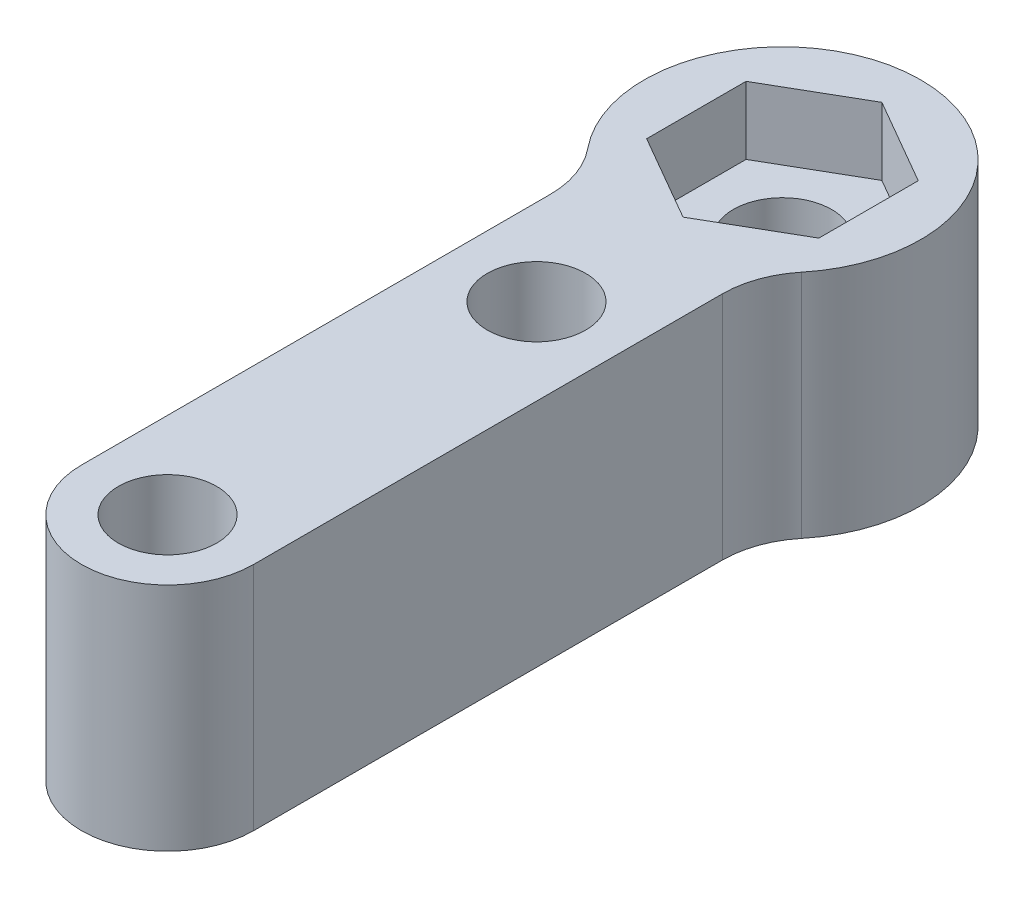
SolidWorks part; units mm, degrees
ref_plane "Front Plane" through (0, 0, 0) normal (0, 0, 1) x (1, 0, 0)
ref_plane "Top Plane" through (0, 0, 0) normal (0, 1, 0) x (1, 0, 0)
ref_plane "Right Plane" through (0, 0, 0) normal (1, 0, 0) x (0, 0, -1)
sketch "Sketch1" plane through (0, 0, 0) normal (0, 1, 0) x (1, 0, 0)
  line L0 (0, 0) -> (0, 12) construction
  line L1 (0, 12) -> (0, 20) construction
  line L2 (-2.8, 0) -> (-2.8, 16.4772)
  line L3 (0, 23.2332) -> (-2.8, 21.6166) construction
  line L4 (-2.8, 21.6166) -> (-2.8, 18.3834) construction
  line L5 (-2.8, 18.3834) -> (0, 16.7668) construction
  line L6 (0, 16.7668) -> (2.8, 18.3834) construction
  line L7 (2.8, 18.3834) -> (2.8, 21.6166) construction
  line L8 (2.8, 21.6166) -> (0, 23.2332) construction
  line L9 (2.8, 0) -> (2.8, 16.4772)
  circle A0 centre (0, 0) radius 1.6
  circle A1 centre (0, 12) radius 1.6
  circle A2 centre (0, 20) radius 1.6
  circle A3 centre (0, 20) radius 2.8 construction
  arc A4 (2.8, 16.4772) -> (-2.8, 16.4772) centre (0, 20) ccw
  arc A5 (-2.8, 0) -> (2.8, 0) centre (0, 0) ccw
  dimension "D3" = 3.2
  dimension "D5" = 4.5
  dimension "D1" = 12
  dimension "D2" = 8
  dimension "D4" = 5.6
extrude "Boss-Extrude1" add sketch "Sketch1" along normal blind 7.5
sketch "Sketch2" plane through (0, 7.5, 0) normal (0, 1, 0) x (1, 0, 0)
  line L1 (0, 23.2332) -> (-2.8, 21.6166)
  line L2 (-2.8, 21.6166) -> (-2.8, 18.3834)
  line L3 (-2.8, 18.3834) -> (0, 16.7668)
  line L4 (0, 16.7668) -> (2.8, 18.3834)
  line L5 (2.8, 18.3834) -> (2.8, 21.6166)
  line L6 (2.8, 21.6166) -> (0, 23.2332)
  circle A0 centre (0, 20) radius 2.8 construction
  circle A1 centre (0, 20) radius 1.6 construction
  dimension "D1" = 5.6
extrude "Cut-Extrude1" cut sketch "Sketch2" against normal blind 2.2
fillet "Fillet1" radius 3 2 edges at (-2.8, 3.75, -16.4772) (2.8, 3.75, -16.4772)
